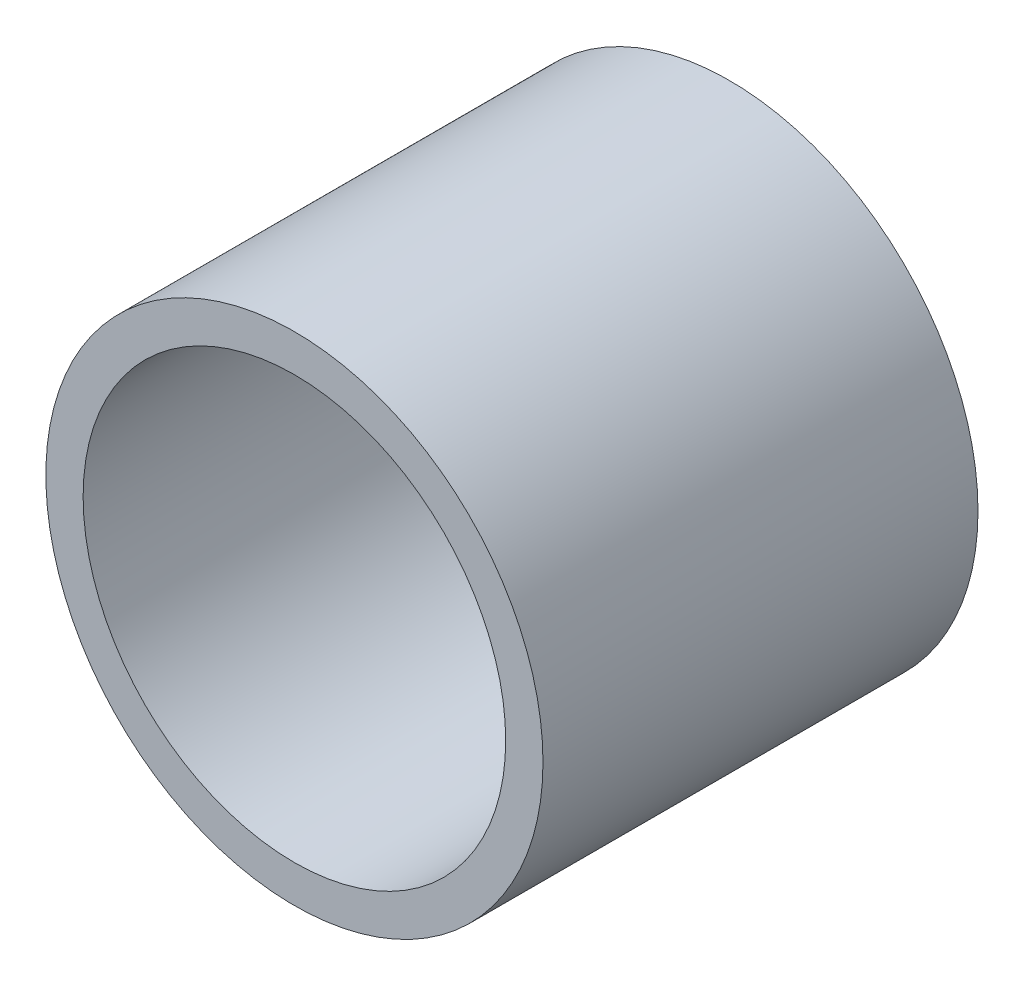
SolidWorks part; units mm, degrees
ref_plane "Front Plane" through (0, 0, 0) normal (0, 0, 1) x (1, 0, 0)
ref_plane "Top Plane" through (0, 0, 0) normal (0, 1, 0) x (1, 0, 0)
ref_plane "Right Plane" through (0, 0, 0) normal (1, 0, 0) x (0, 0, -1)
sketch "Sketch1" plane through (0, 0, 0) normal (0, 0, 1) x (1, 0, 0)
  circle A0 centre (0, 0) radius 25.4
  circle A1 centre (0, 0) radius 21.59
  dimension "D1" = 50.8
  dimension "D2" = 3.81
extrude "Boss-Extrude1" add sketch "Sketch1" along normal blind 44.45
